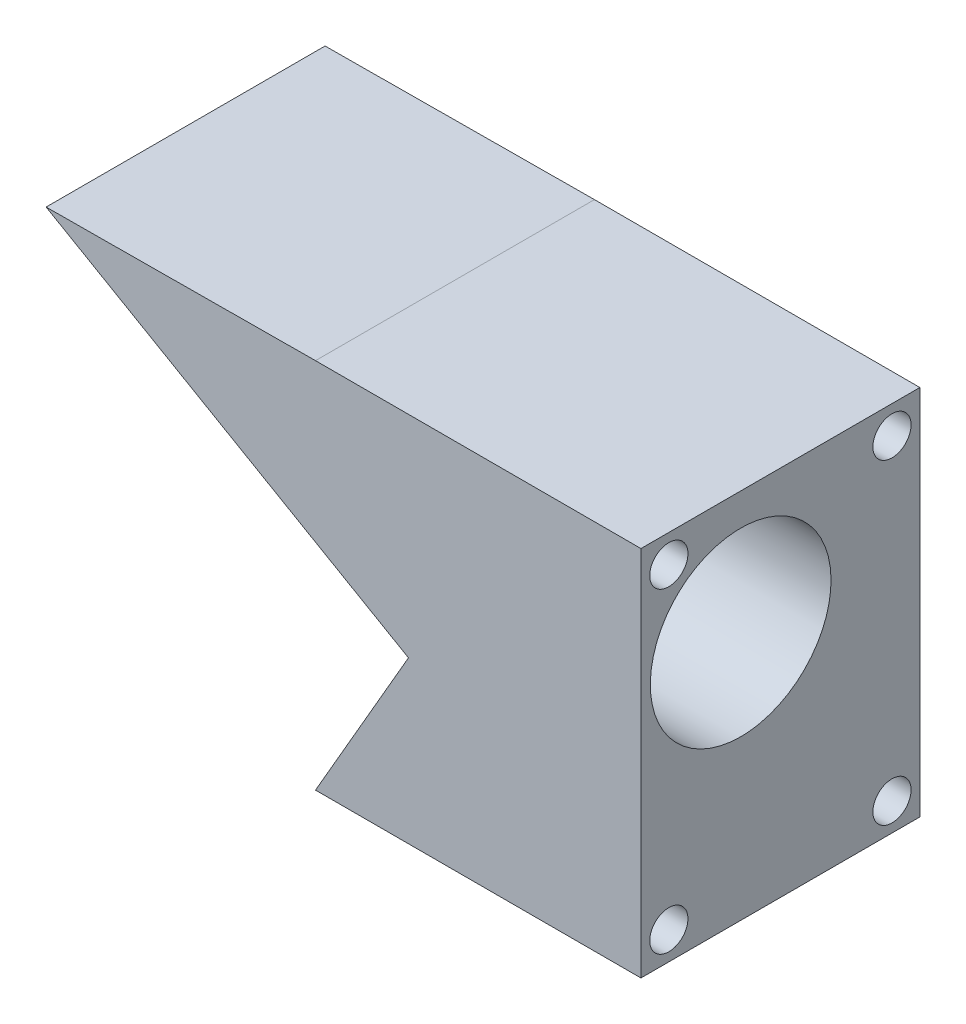
SolidWorks part; units mm, degrees
ref_plane "Front Plane" through (0, 0, 0) normal (0, 0, 1) x (1, 0, 0)
ref_plane "Top Plane" through (0, 0, 0) normal (0, 1, 0) x (1, 0, 0)
ref_plane "Right Plane" through (0, 0, 0) normal (1, 0, 0) x (0, 0, -1)
sketch "Sketch2" plane through (0, 0, 0) normal (0, 0, 1) x (1, 0, 0)
  line L1 (-40.5201, 26.3548) -> (3.9299, 26.3548)
  line L2 (-40.5201, 26.3548) -> (-40.5201, -24.4452)
  line L3 (-40.5201, -24.4452) -> (3.9299, -24.4452)
  line L4 (3.9299, 26.3548) -> (3.9299, -24.4452)
  dimension "D1" = 44.45
  dimension "D2" = 50.8
extrude "Boss-Extrude2" add sketch "Sketch2" along normal blind 38.1
hole_wizard "#5 (0.2055) Diameter Hole1" positions "3DSketch1" profile "Sketch4" hole size "#5" standard "ANSI Inch"
sketch3d "3DSketch1"
  line L0 (3.9299, 26.3548, 19.05) -> (3.9299, -24.4452, 19.05) construction
  line L1 (3.9299, 26.3548, 38.1) -> (3.9299, 26.3548, 0) construction
  line L2 (3.9299, -24.4452, 38.1) -> (3.9299, -24.4452, 0) construction
  line L4 (3.9299, 0.9548, 38.1) -> (3.9299, 0.9548, 0) construction
  line L5 (3.9299, -24.4452, 38.1) -> (3.9299, 26.3548, 38.1) construction
  line L6 (3.9299, -24.4452, 0) -> (3.9299, 26.3548, 0) construction
  point P0 (3.9299, 22.5448, 34.29)
  point P33 (3.9299, 22.5448, 3.81)
  point P35 (3.9299, -20.6352, 3.81)
  point P37 (3.9299, -20.6352, 34.29)
  dimension "D1" = 3.81
  dimension "D2" = 3.81
  dimension "D3" = 3.81
  dimension "D4" = 3.81
  dimension "D5" = 3.81
  dimension "D6" = 3.81
  dimension "D7" = 3.81
  dimension "D8" = 3.81
sketch "Sketch4" plane through (3.9299, 22.5448, 34.29) normal (0, 1, 0) x (0, 0, -1)
  line L0 (0, 0) -> (0, 14.2682)
  line L1 (0, 14.2682) -> (2.6098, 12.7)
  line L2 (2.6098, 12.7) -> (2.6098, 0)
  line L5 (2.6098, 0) -> (0, 0)
  line L10 (0, 14.2682) -> (-2.6099, 12.7) construction
  line L11 (0, -6.35) -> (0, 107.95) construction
  dimension "Hole Dia." = 5.2197
  dimension "Hole Depth" = 12.7
  dimension "Drill Angle" = 118
sketch "Sketch6" plane through (0, 0, 0) normal (0, 0, -1) x (-1, 0, 0)
  line L0 (40.5201, 26.3548) -> (77.3134, 26.1268)
  line L1 (77.3134, 26.1268) -> (40.5201, 4.8842)
  line L2 (40.5201, 26.3548) -> (40.5201, -24.4452) construction
  line L3 (77.3134, 26.1268) -> (27.8201, -2.4482) construction
  line L4 (40.5201, 4.8842) -> (40.5201, 26.3548)
extrude "Boss-Extrude3" add sketch "Sketch6" against normal blind 38.1
sketch "Sketch7" plane through (0, 0, 0) normal (0, 0, -1) x (-1, 0, 0)
  line L0 (40.5201, 4.8842) -> (27.8201, -2.4482)
  line L1 (27.8201, -2.4482) -> (40.5201, -24.4452)
  line L3 (40.5201, 4.8842) -> (77.3134, 26.1268) construction
  line L4 (40.5201, -24.4452) -> (40.5201, 4.8842)
extrude "Cut-Extrude2" cut sketch "Sketch7" against normal through all
sketch "Sketch3" plane through (3.9299, 0, 0) normal (1, 0, 0) x (0, 0, -1)
  line L0 (-24.4764, 26.3548) -> (-24.4764, -24.4452) construction
  line L3 (-38.1, 0.9548) -> (0, 0.9548) construction
  line L4 (-38.1, -24.4452) -> (-38.1, 26.3548) construction
  line L5 (0, -24.4452) -> (0, 26.3548) construction
  circle A0 centre (-24.4764, 9.619) radius 12.342
extrude "Cut-Extrude1" cut sketch "Sketch3" against normal through all both and the other way through all
